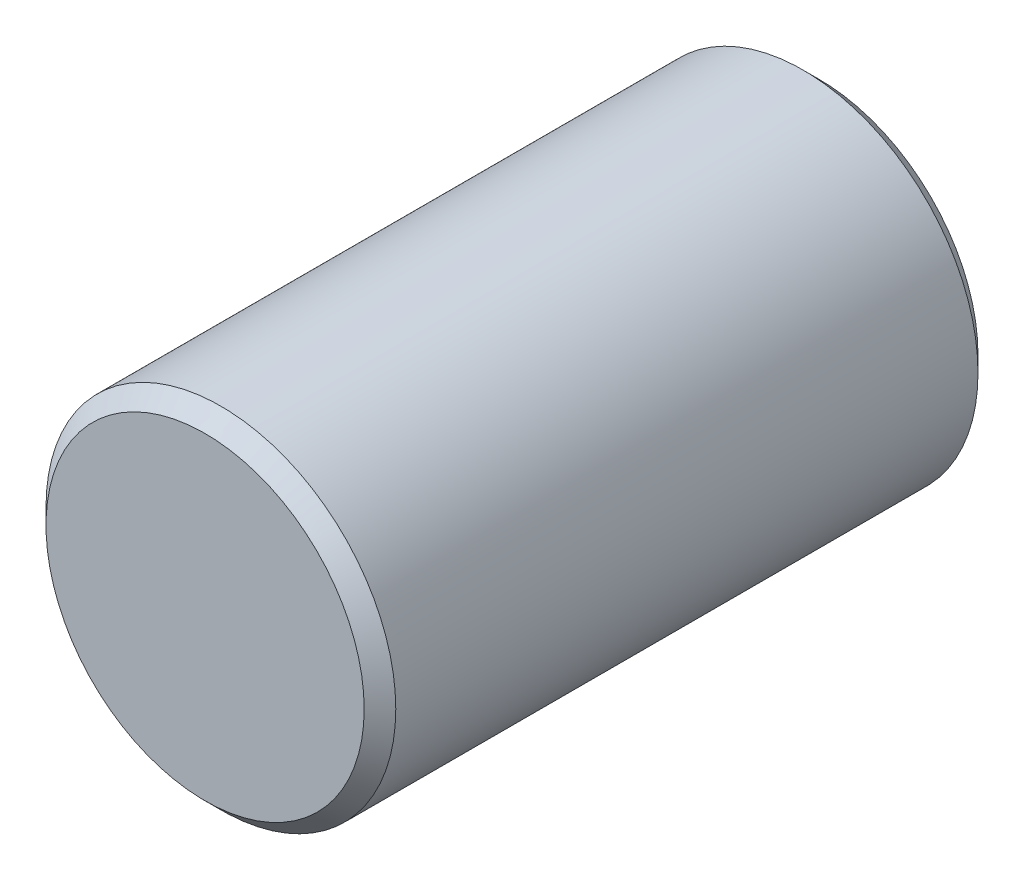
SolidWorks part; units mm, degrees
material "ABS"
ref_plane "Front Plane" through (0, 0, 0) normal (0, 0, 1) x (1, 0, 0)
ref_plane "Top Plane" through (0, 0, 0) normal (0, 1, 0) x (1, 0, 0)
ref_plane "Right Plane" through (0, 0, 0) normal (1, 0, 0) x (0, 0, -1)
sketch "Sketch1" plane through (0, 0, 0) normal (0, 0, 1) x (1, 0, 0)
  circle A0 centre (0, 0) radius 3.875
  dimension "D1" = 7.75
extrude "Boss-Extrude1" add sketch "Sketch1" along normal blind 13.6
chamfer "Chamfer1" distance 0.35 angle 45 2 edges at (3.875, 0, 0) (3.875, 0, 13.6)
ref_plane "Plane1" through (0, 0, 6.8) normal (0, 0, 1) x (1, 0, 0)
